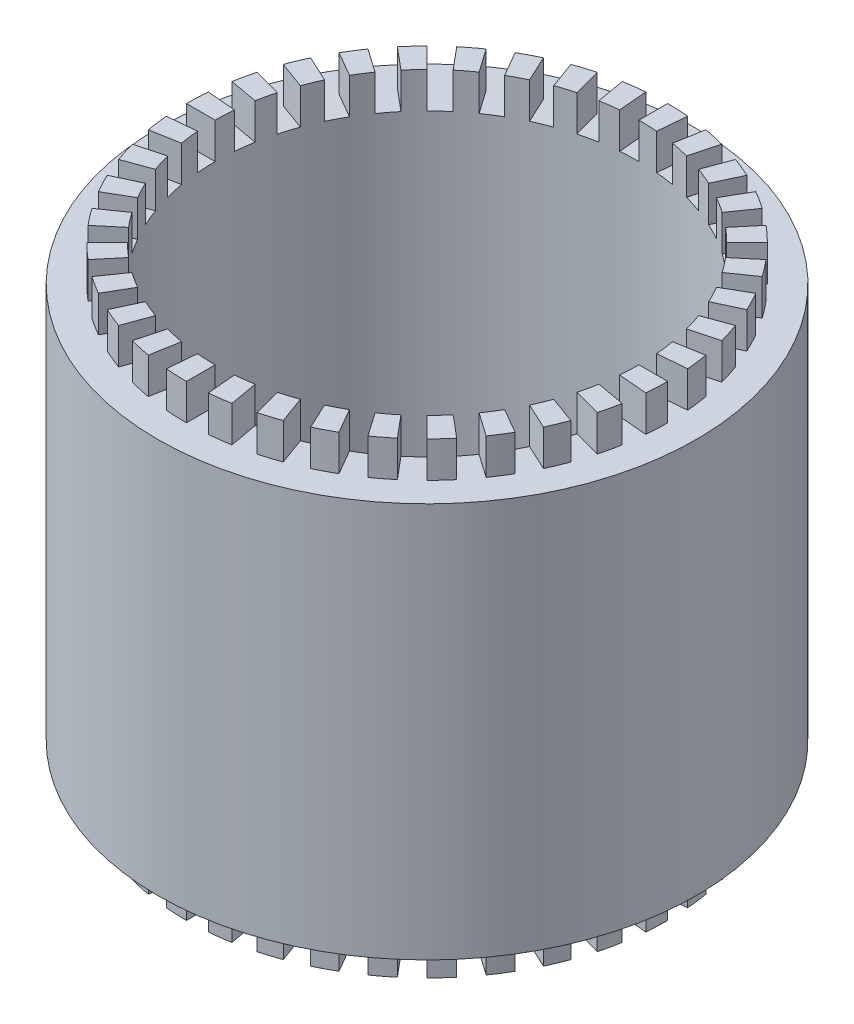
SolidWorks part; units mm, degrees
ref_plane "前视基准面" through (0, 0, 0) normal (0, 0, 1) x (1, 0, 0)
ref_plane "上视基准面" through (0, 0, 0) normal (0, 1, 0) x (1, 0, 0)
ref_plane "右视基准面" through (0, 0, 0) normal (1, 0, 0) x (0, 0, -1)
sketch "Sketch1" plane through (0, 0, 0) normal (0, 1, 0) x (1, 0, 0)
  circle A0 centre (0, 0) radius 26.5 construction
  circle A1 centre (0, 0) radius 29.5
  circle A2 centre (0, 0) radius 37.5
  dimension "D1" = 53
  dimension "D2" = 3
  dimension "D3" = 8
extrude "Boss-Extrude1" add sketch "Sketch1" along normal blind 55
sketch "Sketch2" plane through (0, 55, 0) normal (0, 1, 0) x (1, 0, 0)
  circle A0 centre (0, 0) radius 29.5
  circle A1 centre (0, 0) radius 33.5
  dimension "D1" = 4
extrude "Boss-Extrude2" add sketch "Sketch2" along normal blind 5
sketch "Sketch3" plane through (0, 0, 0) normal (0, -1, 0) x (1, 0, 0)
  circle A0 centre (0, 0) radius 29.5
  circle A1 centre (0, 0) radius 33.5
  dimension "D1" = 4
extrude "Boss-Extrude3" add sketch "Sketch3" along normal blind 5
sketch "Sketch4" plane through (0, -5, 0) normal (0, -1, 0) x (1, 0, 0)
  line L0 (0, 29.5) -> (0, 33.5)
  line L1 (2.5711, 29.3877) -> (2.9197, 33.3725)
  line L2 (5.1226, 29.0518) -> (5.8172, 32.9911)
  line L3 (7.6352, 28.4948) -> (8.6704, 32.3585)
  line L4 (10.0896, 27.7209) -> (11.4577, 31.4797)
  line L5 (12.4672, 26.7361) -> (14.1577, 30.3613)
  line L6 (14.75, 25.5477) -> (16.75, 29.0119)
  line L7 (16.9205, 24.165) -> (19.2148, 27.4416)
  line L8 (18.9622, 22.5983) -> (21.5334, 25.6625)
  line L9 (20.8597, 20.8597) -> (23.6881, 23.6881)
  line L10 (22.5983, 18.9622) -> (25.6625, 21.5334)
  line L11 (24.165, 16.9205) -> (27.4416, 19.2148)
  line L12 (25.5477, 14.75) -> (29.0119, 16.75)
  line L13 (26.7361, 12.4672) -> (30.3613, 14.1577)
  line L14 (27.7209, 10.0896) -> (31.4797, 11.4577)
  line L15 (28.4948, 7.6352) -> (32.3585, 8.6704)
  line L16 (29.0518, 5.1226) -> (32.9911, 5.8172)
  line L17 (29.3877, 2.5711) -> (33.3725, 2.9197)
  line L18 (29.5, 0) -> (33.5, 0)
  line L19 (29.3877, -2.5711) -> (33.3725, -2.9197)
  line L20 (29.0518, -5.1226) -> (32.9911, -5.8172)
  line L21 (28.4948, -7.6352) -> (32.3585, -8.6704)
  line L22 (27.7209, -10.0896) -> (31.4797, -11.4577)
  line L23 (26.7361, -12.4672) -> (30.3613, -14.1577)
  line L24 (25.5477, -14.75) -> (29.0119, -16.75)
  line L25 (24.165, -16.9205) -> (27.4416, -19.2148)
  line L26 (22.5983, -18.9622) -> (25.6625, -21.5334)
  line L27 (20.8597, -20.8597) -> (23.6881, -23.6881)
  line L28 (18.9622, -22.5983) -> (21.5334, -25.6625)
  line L29 (16.9205, -24.165) -> (19.2148, -27.4416)
  line L30 (14.75, -25.5477) -> (16.75, -29.0119)
  line L31 (12.4672, -26.7361) -> (14.1577, -30.3613)
  line L32 (10.0896, -27.7209) -> (11.4577, -31.4797)
  line L33 (7.6352, -28.4948) -> (8.6704, -32.3585)
  line L34 (5.1226, -29.0518) -> (5.8172, -32.9911)
  line L35 (2.5711, -29.3877) -> (2.9197, -33.3725)
  line L36 (0, -29.5) -> (0, -33.5)
  line L37 (-2.5711, -29.3877) -> (-2.9197, -33.3725)
  line L38 (-5.1226, -29.0518) -> (-5.8172, -32.9911)
  line L39 (-7.6352, -28.4948) -> (-8.6704, -32.3585)
  line L40 (-10.0896, -27.7209) -> (-11.4577, -31.4797)
  line L41 (-12.4672, -26.7361) -> (-14.1577, -30.3613)
  line L42 (-14.75, -25.5477) -> (-16.75, -29.0119)
  line L43 (-16.9205, -24.165) -> (-19.2148, -27.4416)
  line L44 (-18.9622, -22.5983) -> (-21.5334, -25.6625)
  line L45 (-20.8597, -20.8597) -> (-23.6881, -23.6881)
  line L46 (-22.5983, -18.9622) -> (-25.6625, -21.5334)
  line L47 (-24.165, -16.9205) -> (-27.4416, -19.2148)
  line L48 (-25.5477, -14.75) -> (-29.0119, -16.75)
  line L49 (-26.7361, -12.4672) -> (-30.3613, -14.1577)
  line L50 (-27.7209, -10.0896) -> (-31.4797, -11.4577)
  line L51 (-28.4948, -7.6352) -> (-32.3585, -8.6704)
  line L52 (-29.0518, -5.1226) -> (-32.9911, -5.8172)
  line L53 (-29.3877, -2.5711) -> (-33.3725, -2.9197)
  line L54 (-29.5, 0) -> (-33.5, 0)
  line L55 (-29.3877, 2.5711) -> (-33.3725, 2.9197)
  line L56 (-29.0518, 5.1226) -> (-32.9911, 5.8172)
  line L57 (-28.4948, 7.6352) -> (-32.3585, 8.6704)
  line L58 (-27.7209, 10.0896) -> (-31.4797, 11.4577)
  line L59 (-26.7361, 12.4672) -> (-30.3613, 14.1577)
  line L60 (-25.5477, 14.75) -> (-29.0119, 16.75)
  line L61 (-24.165, 16.9205) -> (-27.4416, 19.2148)
  line L62 (-22.5983, 18.9622) -> (-25.6625, 21.5334)
  line L63 (-20.8597, 20.8597) -> (-23.6881, 23.6881)
  line L64 (-18.9622, 22.5983) -> (-21.5334, 25.6625)
  line L65 (-16.9205, 24.165) -> (-19.2148, 27.4416)
  line L66 (-14.75, 25.5477) -> (-16.75, 29.0119)
  line L67 (-12.4672, 26.7361) -> (-14.1577, 30.3613)
  line L68 (-10.0896, 27.7209) -> (-11.4577, 31.4797)
  line L69 (-7.6352, 28.4948) -> (-8.6704, 32.3585)
  line L70 (-5.1226, 29.0518) -> (-5.8172, 32.9911)
  line L71 (-2.5711, 29.3877) -> (-2.9197, 33.3725)
  line L72 (2.5711, 29.3877) -> (0, 0) construction
  line L73 (0, 0) -> (0, 29.5) construction
  circle A0 centre (0, 0) radius 33.5 construction
  arc A1 (2.5711, 29.3877) -> (0, 29.5) centre (0, 0) ccw
  circle A2 centre (0, 0) radius 29.5 construction
  arc A3 (2.9197, 33.3725) -> (0, 33.5) centre (0, 0) ccw
  arc A4 (7.6352, 28.4948) -> (5.1226, 29.0518) centre (0, 0) ccw
  arc A5 (8.6704, 32.3585) -> (5.8172, 32.9911) centre (0, 0) ccw
  arc A6 (12.4672, 26.7361) -> (10.0896, 27.7209) centre (0, 0) ccw
  arc A7 (14.1577, 30.3613) -> (11.4577, 31.4797) centre (0, 0) ccw
  arc A8 (16.9205, 24.165) -> (14.75, 25.5477) centre (0, 0) ccw
  arc A9 (19.2148, 27.4416) -> (16.75, 29.0119) centre (0, 0) ccw
  arc A10 (20.8597, 20.8597) -> (18.9622, 22.5983) centre (0, 0) ccw
  arc A11 (23.6881, 23.6881) -> (21.5334, 25.6625) centre (0, 0) ccw
  arc A12 (24.165, 16.9205) -> (22.5983, 18.9622) centre (0, 0) ccw
  arc A13 (27.4416, 19.2148) -> (25.6625, 21.5334) centre (0, 0) ccw
  arc A14 (26.7361, 12.4672) -> (25.5477, 14.75) centre (0, 0) ccw
  arc A15 (30.3613, 14.1577) -> (29.0119, 16.75) centre (0, 0) ccw
  arc A16 (28.4948, 7.6352) -> (27.7209, 10.0896) centre (0, 0) ccw
  arc A17 (32.3585, 8.6704) -> (31.4797, 11.4577) centre (0, 0) ccw
  arc A18 (29.3877, 2.5711) -> (29.0518, 5.1226) centre (0, 0) ccw
  arc A19 (33.3725, 2.9197) -> (32.9911, 5.8172) centre (0, 0) ccw
  arc A20 (29.3877, -2.5711) -> (29.5, 0) centre (0, 0) ccw
  arc A21 (33.3725, -2.9197) -> (33.5, 0) centre (0, 0) ccw
  arc A22 (28.4948, -7.6352) -> (29.0518, -5.1226) centre (0, 0) ccw
  arc A23 (32.3585, -8.6704) -> (32.9911, -5.8172) centre (0, 0) ccw
  arc A24 (26.7361, -12.4672) -> (27.7209, -10.0896) centre (0, 0) ccw
  arc A25 (30.3613, -14.1577) -> (31.4797, -11.4577) centre (0, 0) ccw
  arc A26 (24.165, -16.9205) -> (25.5477, -14.75) centre (0, 0) ccw
  arc A27 (27.4416, -19.2148) -> (29.0119, -16.75) centre (0, 0) ccw
  arc A28 (20.8597, -20.8597) -> (22.5983, -18.9622) centre (0, 0) ccw
  arc A29 (23.6881, -23.6881) -> (25.6625, -21.5334) centre (0, 0) ccw
  arc A30 (16.9205, -24.165) -> (18.9622, -22.5983) centre (0, 0) ccw
  arc A31 (19.2148, -27.4416) -> (21.5334, -25.6625) centre (0, 0) ccw
  arc A32 (12.4672, -26.7361) -> (14.75, -25.5477) centre (0, 0) ccw
  arc A33 (14.1577, -30.3613) -> (16.75, -29.0119) centre (0, 0) ccw
  arc A34 (7.6352, -28.4948) -> (10.0896, -27.7209) centre (0, 0) ccw
  arc A35 (8.6704, -32.3585) -> (11.4577, -31.4797) centre (0, 0) ccw
  arc A36 (2.5711, -29.3877) -> (5.1226, -29.0518) centre (0, 0) ccw
  arc A37 (2.9197, -33.3725) -> (5.8172, -32.9911) centre (0, 0) ccw
  arc A38 (-2.5711, -29.3877) -> (0, -29.5) centre (0, 0) ccw
  arc A39 (-2.9197, -33.3725) -> (0, -33.5) centre (0, 0) ccw
  arc A40 (-7.6352, -28.4948) -> (-5.1226, -29.0518) centre (0, 0) ccw
  arc A41 (-8.6704, -32.3585) -> (-5.8172, -32.9911) centre (0, 0) ccw
  arc A42 (-12.4672, -26.7361) -> (-10.0896, -27.7209) centre (0, 0) ccw
  arc A43 (-14.1577, -30.3613) -> (-11.4577, -31.4797) centre (0, 0) ccw
  arc A44 (-16.9205, -24.165) -> (-14.75, -25.5477) centre (0, 0) ccw
  arc A45 (-19.2148, -27.4416) -> (-16.75, -29.0119) centre (0, 0) ccw
  arc A46 (-20.8597, -20.8597) -> (-18.9622, -22.5983) centre (0, 0) ccw
  arc A47 (-23.6881, -23.6881) -> (-21.5334, -25.6625) centre (0, 0) ccw
  arc A48 (-24.165, -16.9205) -> (-22.5983, -18.9622) centre (0, 0) ccw
  arc A49 (-27.4416, -19.2148) -> (-25.6625, -21.5334) centre (0, 0) ccw
  arc A50 (-26.7361, -12.4672) -> (-25.5477, -14.75) centre (0, 0) ccw
  arc A51 (-30.3613, -14.1577) -> (-29.0119, -16.75) centre (0, 0) ccw
  arc A52 (-28.4948, -7.6352) -> (-27.7209, -10.0896) centre (0, 0) ccw
  arc A53 (-32.3585, -8.6704) -> (-31.4797, -11.4577) centre (0, 0) ccw
  arc A54 (-29.3877, -2.5711) -> (-29.0518, -5.1226) centre (0, 0) ccw
  arc A55 (-33.3725, -2.9197) -> (-32.9911, -5.8172) centre (0, 0) ccw
  arc A56 (-29.3877, 2.5711) -> (-29.5, 0) centre (0, 0) ccw
  arc A57 (-33.3725, 2.9197) -> (-33.5, 0) centre (0, 0) ccw
  arc A58 (-28.4948, 7.6352) -> (-29.0518, 5.1226) centre (0, 0) ccw
  arc A59 (-32.3585, 8.6704) -> (-32.9911, 5.8172) centre (0, 0) ccw
  arc A60 (-26.7361, 12.4672) -> (-27.7209, 10.0896) centre (0, 0) ccw
  arc A61 (-30.3613, 14.1577) -> (-31.4797, 11.4577) centre (0, 0) ccw
  arc A62 (-24.165, 16.9205) -> (-25.5477, 14.75) centre (0, 0) ccw
  arc A63 (-27.4416, 19.2148) -> (-29.0119, 16.75) centre (0, 0) ccw
  arc A64 (-20.8597, 20.8597) -> (-22.5983, 18.9622) centre (0, 0) ccw
  arc A65 (-23.6881, 23.6881) -> (-25.6625, 21.5334) centre (0, 0) ccw
  arc A66 (-16.9205, 24.165) -> (-18.9622, 22.5983) centre (0, 0) ccw
  arc A67 (-19.2148, 27.4416) -> (-21.5334, 25.6625) centre (0, 0) ccw
  arc A68 (-12.4672, 26.7361) -> (-14.75, 25.5477) centre (0, 0) ccw
  arc A69 (-14.1577, 30.3613) -> (-16.75, 29.0119) centre (0, 0) ccw
  arc A70 (-7.6352, 28.4948) -> (-10.0896, 27.7209) centre (0, 0) ccw
  arc A71 (-8.6704, 32.3585) -> (-11.4577, 31.4797) centre (0, 0) ccw
  arc A72 (-2.5711, 29.3877) -> (-5.1226, 29.0518) centre (0, 0) ccw
  arc A73 (-2.9197, 33.3725) -> (-5.8172, 32.9911) centre (0, 0) ccw
  point P154 (0, 0)
  dimension "D1" = 5
  dimension "D2" = 36
extrude "Cut-Extrude1" cut sketch "Sketch4" against normal up to surface (5 mm away) up to face at (0, 0, 37.5)
sketch "Sketch5" plane through (0, 60, 0) normal (0, 1, 0) x (1, 0, 0)
  line L0 (0, -29.5) -> (0, -33.5)
  line L1 (2.5711, -29.3877) -> (2.9197, -33.3725)
  line L2 (-5.1226, -29.0518) -> (-5.8172, -32.9911)
  line L3 (-2.5711, -29.3877) -> (-2.9197, -33.3725)
  line L4 (-10.0896, -27.7209) -> (-11.4577, -31.4797)
  line L5 (-7.6352, -28.4948) -> (-8.6704, -32.3585)
  line L6 (-14.75, -25.5477) -> (-16.75, -29.0119)
  line L7 (-12.4672, -26.7361) -> (-14.1577, -30.3613)
  line L8 (-18.9622, -22.5983) -> (-21.5334, -25.6625)
  line L9 (-16.9205, -24.165) -> (-19.2148, -27.4416)
  line L10 (-22.5983, -18.9622) -> (-25.6625, -21.5334)
  line L11 (-20.8597, -20.8597) -> (-23.6881, -23.6881)
  line L12 (-25.5477, -14.75) -> (-29.0119, -16.75)
  line L13 (-24.165, -16.9205) -> (-27.4416, -19.2148)
  line L14 (-27.7209, -10.0896) -> (-31.4797, -11.4577)
  line L15 (-26.7361, -12.4672) -> (-30.3613, -14.1577)
  line L16 (-29.0518, -5.1226) -> (-32.9911, -5.8172)
  line L17 (-28.4948, -7.6352) -> (-32.3585, -8.6704)
  line L18 (-29.5, 0) -> (-33.5, 0)
  line L19 (-29.3877, -2.5711) -> (-33.3725, -2.9197)
  line L20 (-29.0518, 5.1226) -> (-32.9911, 5.8172)
  line L21 (-29.3877, 2.5711) -> (-33.3725, 2.9197)
  line L22 (-27.7209, 10.0896) -> (-31.4797, 11.4577)
  line L23 (-28.4948, 7.6352) -> (-32.3585, 8.6704)
  line L24 (-25.5477, 14.75) -> (-29.0119, 16.75)
  line L25 (-26.7361, 12.4672) -> (-30.3613, 14.1577)
  line L26 (-22.5983, 18.9622) -> (-25.6625, 21.5334)
  line L27 (-24.165, 16.9205) -> (-27.4416, 19.2148)
  line L28 (-18.9622, 22.5983) -> (-21.5334, 25.6625)
  line L29 (-20.8597, 20.8597) -> (-23.6881, 23.6881)
  line L30 (-14.75, 25.5477) -> (-16.75, 29.0119)
  line L31 (-16.9205, 24.165) -> (-19.2148, 27.4416)
  line L32 (-10.0896, 27.7209) -> (-11.4577, 31.4797)
  line L33 (-12.4672, 26.7361) -> (-14.1577, 30.3613)
  line L34 (-5.1226, 29.0518) -> (-5.8172, 32.9911)
  line L35 (-7.6352, 28.4948) -> (-8.6704, 32.3585)
  line L36 (0, 29.5) -> (0, 33.5)
  line L37 (-2.5711, 29.3877) -> (-2.9197, 33.3725)
  line L38 (5.1226, 29.0518) -> (5.8172, 32.9911)
  line L39 (2.5711, 29.3877) -> (2.9197, 33.3725)
  line L40 (10.0896, 27.7209) -> (11.4577, 31.4797)
  line L41 (7.6352, 28.4948) -> (8.6704, 32.3585)
  line L42 (14.75, 25.5477) -> (16.75, 29.0119)
  line L43 (12.4672, 26.7361) -> (14.1577, 30.3613)
  line L44 (18.9622, 22.5983) -> (21.5334, 25.6625)
  line L45 (16.9205, 24.165) -> (19.2148, 27.4416)
  line L46 (22.5983, 18.9622) -> (25.6625, 21.5334)
  line L47 (20.8597, 20.8597) -> (23.6881, 23.6881)
  line L48 (25.5477, 14.75) -> (29.0119, 16.75)
  line L49 (24.165, 16.9205) -> (27.4416, 19.2148)
  line L50 (27.7209, 10.0896) -> (31.4797, 11.4577)
  line L51 (26.7361, 12.4672) -> (30.3613, 14.1577)
  line L52 (29.0518, 5.1226) -> (32.9911, 5.8172)
  line L53 (28.4948, 7.6352) -> (32.3585, 8.6704)
  line L54 (29.5, 0) -> (33.5, 0)
  line L55 (29.3877, 2.5711) -> (33.3725, 2.9197)
  line L56 (29.0518, -5.1226) -> (32.9911, -5.8172)
  line L57 (29.3877, -2.5711) -> (33.3725, -2.9197)
  line L58 (27.7209, -10.0896) -> (31.4797, -11.4577)
  line L59 (28.4948, -7.6352) -> (32.3585, -8.6704)
  line L60 (25.5477, -14.75) -> (29.0119, -16.75)
  line L61 (26.7361, -12.4672) -> (30.3613, -14.1577)
  line L62 (22.5983, -18.9622) -> (25.6625, -21.5334)
  line L63 (24.165, -16.9205) -> (27.4416, -19.2148)
  line L64 (18.9622, -22.5983) -> (21.5334, -25.6625)
  line L65 (20.8597, -20.8597) -> (23.6881, -23.6881)
  line L66 (14.75, -25.5477) -> (16.75, -29.0119)
  line L67 (16.9205, -24.165) -> (19.2148, -27.4416)
  line L68 (10.0896, -27.7209) -> (11.4577, -31.4797)
  line L69 (12.4672, -26.7361) -> (14.1577, -30.3613)
  line L70 (5.1226, -29.0518) -> (5.8172, -32.9911)
  line L71 (7.6352, -28.4948) -> (8.6704, -32.3585)
  line L72 (2.5711, -29.3877) -> (0, 0) construction
  line L73 (0, -29.5) -> (0, 0) construction
  circle A1 centre (0, 0) radius 33.5 construction
  arc A3 (0, -33.5) -> (2.9197, -33.3725) centre (0, 0) ccw
  arc A4 (0, -29.5) -> (2.5711, -29.3877) centre (0, 0) ccw
  arc A5 (-5.8172, -32.9911) -> (-2.9197, -33.3725) centre (0, 0) ccw
  arc A6 (-5.1226, -29.0518) -> (-2.5711, -29.3877) centre (0, 0) ccw
  arc A7 (-11.4577, -31.4797) -> (-8.6704, -32.3585) centre (0, 0) ccw
  arc A8 (-10.0896, -27.7209) -> (-7.6352, -28.4948) centre (0, 0) ccw
  arc A9 (-16.75, -29.0119) -> (-14.1577, -30.3613) centre (0, 0) ccw
  arc A10 (-14.75, -25.5477) -> (-12.4672, -26.7361) centre (0, 0) ccw
  arc A11 (-21.5334, -25.6625) -> (-19.2148, -27.4416) centre (0, 0) ccw
  arc A12 (-18.9622, -22.5983) -> (-16.9205, -24.165) centre (0, 0) ccw
  arc A13 (-25.6625, -21.5334) -> (-23.6881, -23.6881) centre (0, 0) ccw
  arc A14 (-22.5983, -18.9622) -> (-20.8597, -20.8597) centre (0, 0) ccw
  arc A15 (-29.0119, -16.75) -> (-27.4416, -19.2148) centre (0, 0) ccw
  arc A16 (-25.5477, -14.75) -> (-24.165, -16.9205) centre (0, 0) ccw
  arc A17 (-31.4797, -11.4577) -> (-30.3613, -14.1577) centre (0, 0) ccw
  arc A18 (-27.7209, -10.0896) -> (-26.7361, -12.4672) centre (0, 0) ccw
  arc A19 (-32.9911, -5.8172) -> (-32.3585, -8.6704) centre (0, 0) ccw
  arc A20 (-29.0518, -5.1226) -> (-28.4948, -7.6352) centre (0, 0) ccw
  arc A21 (-33.5, 0) -> (-33.3725, -2.9197) centre (0, 0) ccw
  arc A22 (-29.5, 0) -> (-29.3877, -2.5711) centre (0, 0) ccw
  arc A23 (-32.9911, 5.8172) -> (-33.3725, 2.9197) centre (0, 0) ccw
  arc A24 (-29.0518, 5.1226) -> (-29.3877, 2.5711) centre (0, 0) ccw
  arc A25 (-31.4797, 11.4577) -> (-32.3585, 8.6704) centre (0, 0) ccw
  arc A26 (-27.7209, 10.0896) -> (-28.4948, 7.6352) centre (0, 0) ccw
  arc A27 (-29.0119, 16.75) -> (-30.3613, 14.1577) centre (0, 0) ccw
  arc A28 (-25.5477, 14.75) -> (-26.7361, 12.4672) centre (0, 0) ccw
  arc A29 (-25.6625, 21.5334) -> (-27.4416, 19.2148) centre (0, 0) ccw
  arc A30 (-22.5983, 18.9622) -> (-24.165, 16.9205) centre (0, 0) ccw
  arc A31 (-21.5334, 25.6625) -> (-23.6881, 23.6881) centre (0, 0) ccw
  arc A32 (-18.9622, 22.5983) -> (-20.8597, 20.8597) centre (0, 0) ccw
  arc A33 (-16.75, 29.0119) -> (-19.2148, 27.4416) centre (0, 0) ccw
  arc A34 (-14.75, 25.5477) -> (-16.9205, 24.165) centre (0, 0) ccw
  arc A35 (-11.4577, 31.4797) -> (-14.1577, 30.3613) centre (0, 0) ccw
  arc A36 (-10.0896, 27.7209) -> (-12.4672, 26.7361) centre (0, 0) ccw
  arc A37 (-5.8172, 32.9911) -> (-8.6704, 32.3585) centre (0, 0) ccw
  arc A38 (-5.1226, 29.0518) -> (-7.6352, 28.4948) centre (0, 0) ccw
  arc A39 (0, 33.5) -> (-2.9197, 33.3725) centre (0, 0) ccw
  arc A40 (0, 29.5) -> (-2.5711, 29.3877) centre (0, 0) ccw
  arc A41 (5.8172, 32.9911) -> (2.9197, 33.3725) centre (0, 0) ccw
  arc A42 (5.1226, 29.0518) -> (2.5711, 29.3877) centre (0, 0) ccw
  arc A43 (11.4577, 31.4797) -> (8.6704, 32.3585) centre (0, 0) ccw
  arc A44 (10.0896, 27.7209) -> (7.6352, 28.4948) centre (0, 0) ccw
  arc A45 (16.75, 29.0119) -> (14.1577, 30.3613) centre (0, 0) ccw
  arc A46 (14.75, 25.5477) -> (12.4672, 26.7361) centre (0, 0) ccw
  arc A47 (21.5334, 25.6625) -> (19.2148, 27.4416) centre (0, 0) ccw
  arc A48 (18.9622, 22.5983) -> (16.9205, 24.165) centre (0, 0) ccw
  arc A49 (25.6625, 21.5334) -> (23.6881, 23.6881) centre (0, 0) ccw
  arc A50 (22.5983, 18.9622) -> (20.8597, 20.8597) centre (0, 0) ccw
  arc A51 (29.0119, 16.75) -> (27.4416, 19.2148) centre (0, 0) ccw
  arc A52 (25.5477, 14.75) -> (24.165, 16.9205) centre (0, 0) ccw
  arc A53 (31.4797, 11.4577) -> (30.3613, 14.1577) centre (0, 0) ccw
  arc A54 (27.7209, 10.0896) -> (26.7361, 12.4672) centre (0, 0) ccw
  arc A55 (32.9911, 5.8172) -> (32.3585, 8.6704) centre (0, 0) ccw
  arc A56 (29.0518, 5.1226) -> (28.4948, 7.6352) centre (0, 0) ccw
  arc A57 (33.5, 0) -> (33.3725, 2.9197) centre (0, 0) ccw
  arc A58 (29.5, 0) -> (29.3877, 2.5711) centre (0, 0) ccw
  arc A59 (32.9911, -5.8172) -> (33.3725, -2.9197) centre (0, 0) ccw
  arc A60 (29.0518, -5.1226) -> (29.3877, -2.5711) centre (0, 0) ccw
  arc A61 (31.4797, -11.4577) -> (32.3585, -8.6704) centre (0, 0) ccw
  arc A62 (27.7209, -10.0896) -> (28.4948, -7.6352) centre (0, 0) ccw
  arc A63 (29.0119, -16.75) -> (30.3613, -14.1577) centre (0, 0) ccw
  arc A64 (25.5477, -14.75) -> (26.7361, -12.4672) centre (0, 0) ccw
  arc A65 (25.6625, -21.5334) -> (27.4416, -19.2148) centre (0, 0) ccw
  arc A66 (22.5983, -18.9622) -> (24.165, -16.9205) centre (0, 0) ccw
  arc A67 (21.5334, -25.6625) -> (23.6881, -23.6881) centre (0, 0) ccw
  arc A68 (18.9622, -22.5983) -> (20.8597, -20.8597) centre (0, 0) ccw
  arc A69 (16.75, -29.0119) -> (19.2148, -27.4416) centre (0, 0) ccw
  arc A70 (14.75, -25.5477) -> (16.9205, -24.165) centre (0, 0) ccw
  arc A71 (11.4577, -31.4797) -> (14.1577, -30.3613) centre (0, 0) ccw
  arc A72 (10.0896, -27.7209) -> (12.4672, -26.7361) centre (0, 0) ccw
  arc A73 (5.8172, -32.9911) -> (8.6704, -32.3585) centre (0, 0) ccw
  arc A74 (5.1226, -29.0518) -> (7.6352, -28.4948) centre (0, 0) ccw
  point P150 (0, 0)
  point P152 (0, 0)
  dimension "D1" = 5
  dimension "D2" = 36
extrude "Cut-Extrude2" cut sketch "Sketch5" against normal up to surface (5 mm away) up to face at (0, 55, 37.5)
